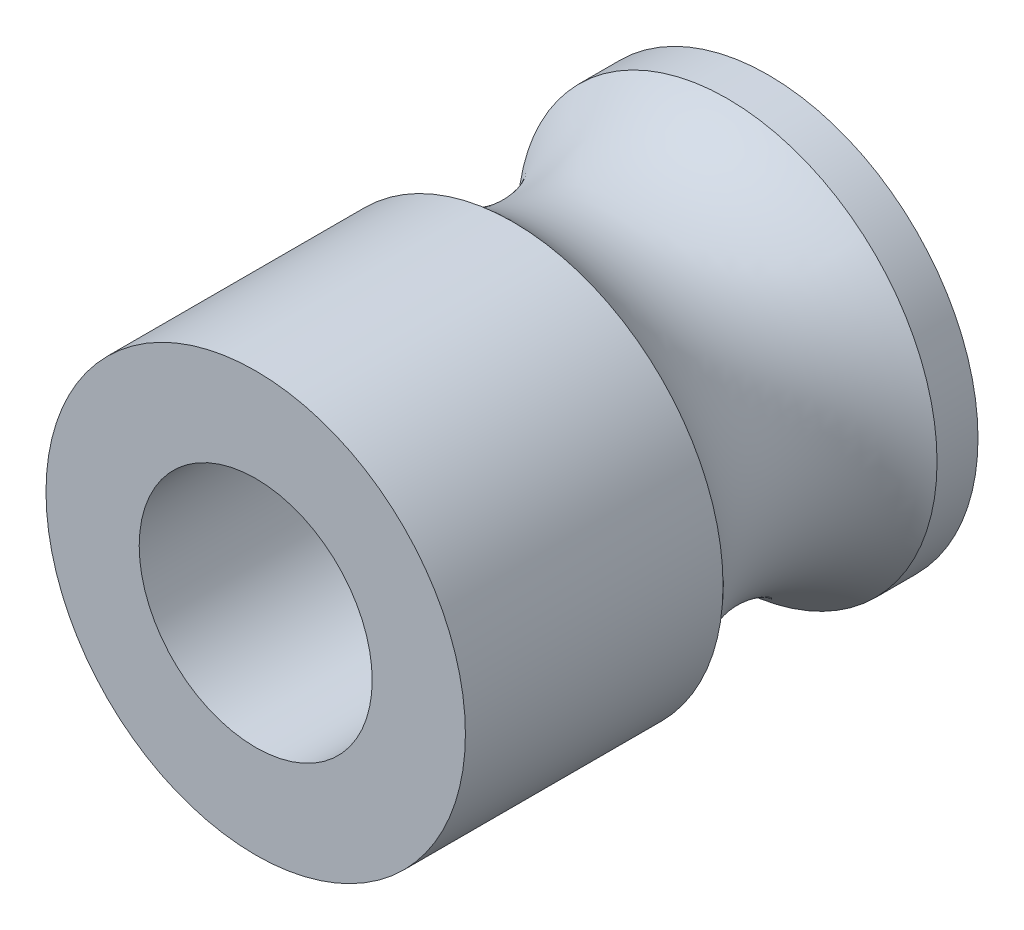
SolidWorks part; units mm, degrees
ref_plane "Front Plane" through (0, 0, 0) normal (0, 0, 1) x (1, 0, 0)
ref_plane "Top Plane" through (0, 0, 0) normal (0, 1, 0) x (1, 0, 0)
ref_plane "Right Plane" through (0, 0, 0) normal (1, 0, 0) x (0, 0, -1)
sketch "Sketch1" plane through (0, 0, 0) normal (0, 1, 0) x (1, 0, 0)
  line L0 (4.5, 0) -> (0, 0)
  line L1 (0, 0) -> (0, -11)
  line L2 (0, -11) -> (4.5, -11)
  line L3 (4.5, -11) -> (4.5, -5.4712)
  line L4 (4.5, -0.8788) -> (4.5, 0)
  line L5 (0, 0) -> (0, -11) construction
  arc A0 (4.5, -5.4712) -> (4.5, -0.8788) centre (6.8, -3.175) cw
  dimension "D4" = 3.55
  dimension "D5" = 3.25
  dimension "D1" = 4.5
  dimension "D2" = 11
  dimension "D3" = 3.175
revolve "Revolve1" add sketch "Sketch1" angle 360 about L5
hole_wizard "Ø5.0 (5) Diameter Hole1" positions "Sketch3" profile "Sketch2" hole size "Ø5.0" standard "ANSI Metric"
sketch "Sketch3" plane through (0, 0, 11) normal (0, 0, 1) x (1, 0, 0)
  point P0 (0, 0)
sketch "Sketch2" plane through (0, 0, 11) normal (1, 0, 0) x (0, -1, 0)
  line L0 (0, 0) -> (0, 11)
  line L1 (0, 11) -> (2.5, 11)
  line L2 (2.5, 11) -> (2.5, 0)
  line L5 (2.5, 0) -> (0, 0)
  line L11 (0, -6.35) -> (0, 107.95) construction
  dimension "Thru Hole Dia." = 5
  dimension "Thru Hole Depth" = 11
